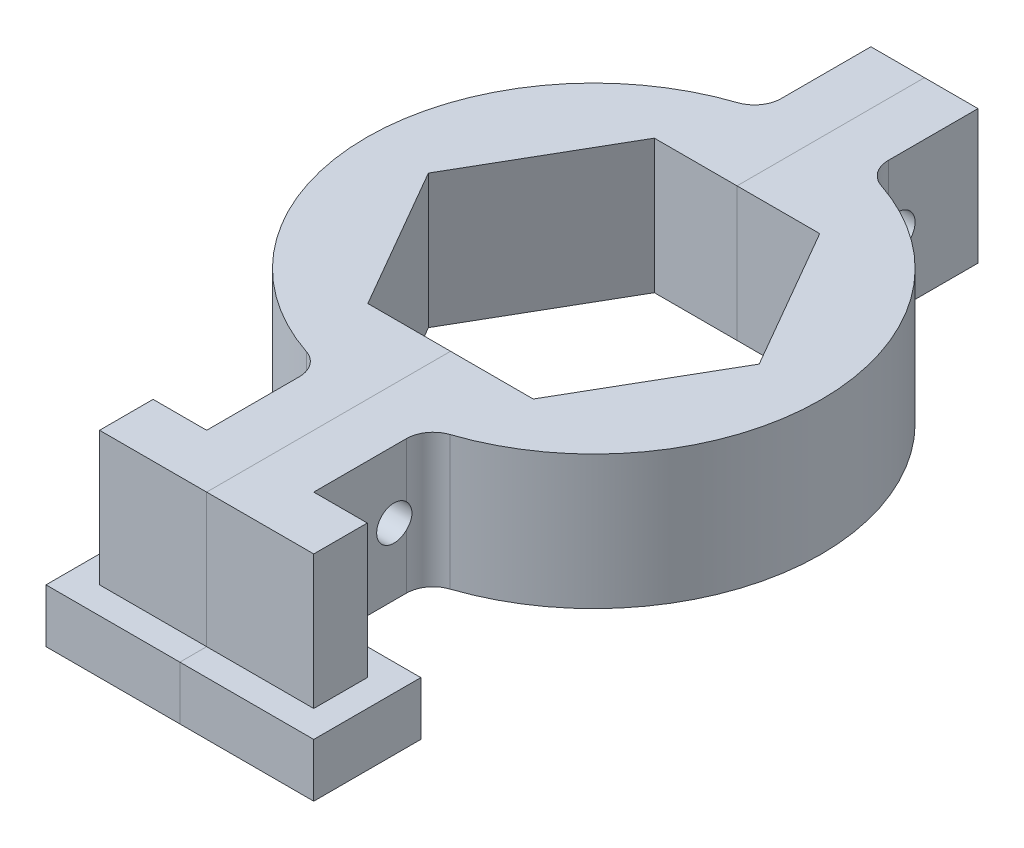
SolidWorks part; units mm, degrees
ref_plane "Front Plane" through (0, 0, 0) normal (0, 0, 1) x (1, 0, 0)
ref_plane "Top Plane" through (0, 0, 0) normal (0, 1, 0) x (1, 0, 0)
ref_plane "Right Plane" through (0, 0, 0) normal (1, 0, 0) x (0, 0, -1)
sketch "Sketch1" plane through (0, 0, 0) normal (0, 1, 0) x (1, 0, 0)
  line L2 (0, 13.589) -> (-7.8456, 13.589)
  line L3 (-7.8456, 13.589) -> (-15.6912, 0)
  line L4 (-15.6912, 0) -> (-7.8456, -13.589)
  line L5 (-7.8456, -13.589) -> (0, -13.589)
  line L12 (0, 18.669) -> (0, -18.669)
  line L21 (15.6912, 0) -> (11.7684, 6.7945) [skipped]
  line L22 (11.7684, -6.7945) -> (15.6912, 0) [skipped]
  line L23 (-5.08, 13.589) -> (-5.08, -13.589)
  line L24 (0, 31.369) -> (-5.08, 31.369)
  line L25 (0, 31.369) -> (0, -36.7284)
  line L26 (0, -36.7284) -> (-5.08, -36.7284)
  line L27 (-5.08, 31.369) -> (-5.08, 22.8606)
  line L28 (0, -36.7284) -> (-10.16, -36.7284)
  line L29 (0, -36.7284) -> (0, -31.6484)
  line L30 (-5.08, -31.6484) -> (-10.16, -31.6484)
  line L31 (-10.16, -36.7284) -> (-10.16, -31.6484)
  line L34 (-5.08, -22.8606) -> (-5.08, -31.6484)
  arc A0 (0, 13.589) -> (0, -13.589) centre (0, 0) ccw construction
  arc A1 (-6.8168, 20.4509) -> (-6.8168, -20.4509) centre (0, 0) ccw
  arc A2 (-6.8168, 20.4509) -> (-5.08, 22.8606) centre (-7.62, 22.8606) ccw
  arc A3 (-5.08, -22.8606) -> (-6.8168, -20.4509) centre (-7.62, -22.8606) ccw
  dimension "D2" = 2.54
  dimension "D1" = 27.178
  dimension "D3" = 5.08
  dimension "D4" = 10.16
  dimension "D5" = 5.08
  dimension "D6" = 36.7284
extrude "Boss-Extrude1" add sketch "Sketch1" along normal blind 12.7 contours A3 L34 L30 L31 L28 L26 L25 L12 L5 L4 L3 L2 L24 L27 A2 A1
sketch "Sketch2" plane through (-5.08, 0, 0) normal (-1, 0, 0) x (0, 0, 1)
  line L0 (-31.369, 12.7) -> (-16.129, 0) construction
  line L1 (31.6484, 12.7) -> (16.4084, 0) construction
  circle A0 centre (-23.749, 6.35) radius 1.651
  circle A1 centre (24.0284, 6.35) radius 1.651
  line M16 (-22.8606, 0) -> (-22.8606, 12.7)
  dimension "D1" = 3.302
  dimension "D2" = 3.302
  dimension "D3" = 15.24
  dimension "D4" = 15.24
extrude "Cut-Extrude1" cut sketch "Sketch2" against normal through all both and the other way through all contours A0 M16 | A0 M16 | A1
sketch "Sketch3" plane through (0, 0, 0) normal (0, -1, 0) x (1, 0, 0)
  line L0 (0, 13.589) -> (0, 36.7284) construction
  line L1 (0, 29.1084) -> (-12.7, 29.1084)
  line L2 (0, 29.1084) -> (0, 39.2684)
  line L3 (0, 39.2684) -> (-12.7, 39.2684)
  line L4 (-12.7, 29.1084) -> (-12.7, 39.2684)
  line L5 (0, 36.7284) -> (-10.16, 36.7284) construction
  line L6 (-10.16, 36.7284) -> (-10.16, 31.6484) construction
  line L7 (-5.08, 31.6484) -> (-10.16, 31.6484) construction
  dimension "D1" = 2.54
  dimension "D2" = 2.54
  dimension "D3" = 2.54
extrude "Boss-Extrude2" add sketch "Sketch3" along normal blind 5.08
mirror "Mirror1" about plane through (0, 12.7, 0) normal (1, 0, 0) of bodies 103
